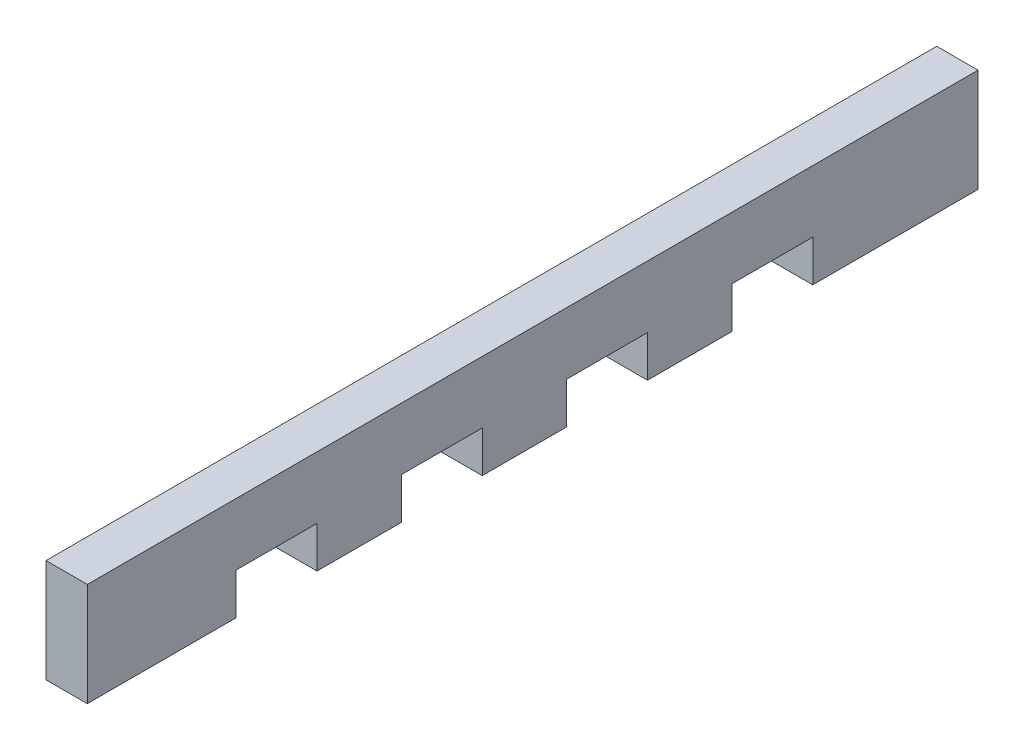
SolidWorks part; units mm, degrees
ref_plane "Front Plane" through (0, 0, 0) normal (0, 0, 1) x (1, 0, 0)
ref_plane "Top Plane" through (0, 0, 0) normal (0, 1, 0) x (1, 0, 0)
ref_plane "Right Plane" through (0, 0, 0) normal (1, 0, 0) x (0, 0, -1)
sketch "Sketch1" plane through (0, 0, 0) normal (1, 0, 0) x (0, 0, -1)
  line L0 (0, 0) -> (22.86, 0)
  line L1 (22.86, 0) -> (22.86, 6.35)
  line L2 (22.86, 6.35) -> (35.306, 6.35)
  line L3 (35.306, 6.35) -> (35.306, 0)
  line L4 (35.306, 0) -> (48.26, 0)
  line L5 (48.26, 0) -> (48.26, 6.35)
  line L6 (48.26, 6.35) -> (60.706, 6.35)
  line L7 (60.706, 6.35) -> (60.706, 0)
  line L8 (60.706, 0) -> (73.66, 0)
  line L9 (73.66, 0) -> (73.66, 6.35)
  line L10 (73.66, 6.35) -> (86.106, 6.35)
  line L11 (86.106, 6.35) -> (86.106, 0)
  line L12 (86.106, 0) -> (99.06, 0)
  line L13 (99.06, 0) -> (99.06, 6.35)
  line L14 (99.06, 6.35) -> (111.506, 6.35)
  line L15 (111.506, 6.35) -> (111.506, 0)
  line L16 (111.506, 0) -> (136.906, 0)
  line L17 (136.906, 0) -> (136.906, 15.875)
  line L18 (136.906, 15.875) -> (0, 15.875)
  line L19 (0, 15.875) -> (0, 0)
  line L33 (111.506, 0) -> (124.46, 0) [skipped]
  dimension "D1" = 12.446
  dimension "D2" = 12.954
  dimension "D3" = 6.35
  dimension "D4" = 22.86
  dimension "D5" = 4
  dimension "D7" = 15.875
  dimension "D6" = 25.4
extrude "Boss-Extrude1" add sketch "Sketch1" along normal blind 6.35
